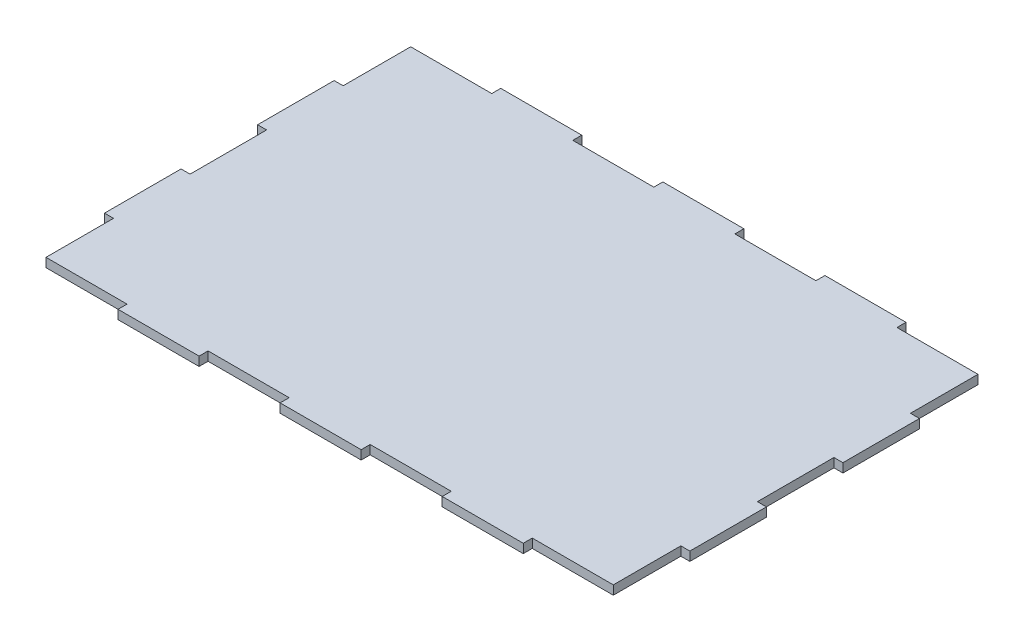
SolidWorks part; units mm, degrees
material "A-Glass Fiber"
ref_plane "Front Plane" through (0, 0, 0) normal (0, 0, 1) x (1, 0, 0)
ref_plane "Top Plane" through (0, 0, 0) normal (0, 1, 0) x (1, 0, 0)
ref_plane "Right Plane" through (0, 0, 0) normal (1, 0, 0) x (0, 0, -1)
sketch "Sketch1" plane through (0, 0, 0) normal (0, 1, 0) x (1, 0, 0)
  line L4 (45.72, 215.9) -> (-45.72, 215.9)
  line L5 (-45.72, 215.9) -> (-45.72, 205.74)
  line L6 (-45.72, 205.74) -> (45.72, 205.74)
  line L7 (45.72, 205.74) -> (45.72, 215.9)
  line L8 (228.6, 215.9) -> (137.16, 215.9)
  line L9 (137.16, 215.9) -> (137.16, 205.74)
  line L10 (137.16, 205.74) -> (228.6, 205.74)
  line L11 (228.6, 205.74) -> (228.6, 215.9)
  line L12 (330.2, 43.18) -> (330.2, 129.54)
  line L13 (330.2, 129.54) -> (320.04, 129.54)
  line L15 (320.04, 43.18) -> (330.2, 43.18)
  line L16 (330.2, -129.54) -> (330.2, -43.18)
  line L17 (330.2, -43.18) -> (320.04, -43.18)
  line L18 (320.04, -43.18) -> (320.04, -129.54)
  line L19 (320.04, -129.54) -> (330.2, -129.54)
  line L20 (228.6, -205.74) -> (137.16, -205.74)
  line L21 (137.16, -205.74) -> (137.16, -215.9)
  line L22 (137.16, -215.9) -> (228.6, -215.9)
  line L23 (228.6, -215.9) -> (228.6, -205.74)
  line L24 (45.72, -205.74) -> (-45.72, -205.74)
  line L25 (-45.72, -205.74) -> (-45.72, -215.9)
  line L26 (-45.72, -215.9) -> (45.72, -215.9)
  line L27 (45.72, -215.9) -> (45.72, -205.74)
  line L28 (-137.16, -205.74) -> (-228.6, -205.74)
  line L29 (-228.6, -205.74) -> (-228.6, -215.9)
  line L30 (-228.6, -215.9) -> (-137.16, -215.9)
  line L31 (-137.16, -215.9) -> (-137.16, -205.74)
  line L32 (-137.16, 215.9) -> (-228.6, 215.9)
  line L33 (-228.6, 215.9) -> (-228.6, 205.74)
  line L34 (-228.6, 205.74) -> (-137.16, 205.74)
  line L35 (-137.16, 205.74) -> (-137.16, 215.9)
  line L36 (-320.04, -129.54) -> (-320.04, -43.18)
  line L37 (-320.04, -43.18) -> (-330.2, -43.18)
  line L38 (-330.2, -43.18) -> (-330.2, -129.54)
  line L39 (-330.2, -129.54) -> (-320.04, -129.54)
  line L40 (-320.04, 43.18) -> (-320.04, 129.54)
  line L41 (-320.04, 129.54) -> (-330.2, 129.54)
  line L42 (-330.2, 129.54) -> (-330.2, 43.18)
  line L43 (-330.2, 43.18) -> (-320.04, 43.18)
  line L45 (-320.04, -205.74) -> (-330.2, -205.74)
  line L46 (228.6, -205.74) -> (320.04, -205.74)
  line L47 (320.04, 205.74) -> (330.2, 205.74)
  line L49 (330.2, 215.9) -> (330.2, -215.9)
  line L50 (330.2, -215.9) -> (-330.2, -215.9)
  line L51 (-330.2, 215.9) -> (-330.2, -215.9)
  line L52 (45.72, 215.9) -> (-45.72, 215.9)
  line L53 (-45.72, 215.9) -> (-45.72, 205.74)
  line L54 (-45.72, 205.74) -> (45.72, 205.74)
  line L55 (45.72, 205.74) -> (45.72, 215.9)
  line L56 (228.6, 215.9) -> (137.16, 215.9)
  line L57 (137.16, 215.9) -> (137.16, 205.74)
  line L58 (137.16, 205.74) -> (228.6, 205.74)
  line L59 (228.6, 205.74) -> (228.6, 215.9)
  line L60 (330.2, 43.18) -> (330.2, 129.54)
  line L61 (330.2, 129.54) -> (320.04, 129.54)
  line L62 (320.04, 129.54) -> (320.04, 43.18)
  line L63 (320.04, 43.18) -> (330.2, 43.18)
  line L64 (330.2, -129.54) -> (330.2, -43.18)
  line L65 (330.2, -43.18) -> (320.04, -43.18)
  line L66 (320.04, -43.18) -> (320.04, -129.54)
  line L67 (320.04, -129.54) -> (330.2, -129.54)
  line L68 (228.6, -205.74) -> (137.16, -205.74)
  line L69 (137.16, -205.74) -> (137.16, -215.9)
  line L70 (137.16, -215.9) -> (228.6, -215.9)
  line L71 (228.6, -215.9) -> (228.6, -205.74)
  line L72 (45.72, -205.74) -> (-45.72, -205.74)
  line L73 (-45.72, -205.74) -> (-45.72, -215.9)
  line L74 (-45.72, -215.9) -> (45.72, -215.9)
  line L75 (45.72, -215.9) -> (45.72, -205.74)
  line L76 (-137.16, -205.74) -> (-228.6, -205.74)
  line L77 (-228.6, -205.74) -> (-228.6, -215.9)
  line L78 (-228.6, -215.9) -> (-137.16, -215.9)
  line L79 (-137.16, -215.9) -> (-137.16, -205.74)
  line L80 (-137.16, 215.9) -> (-228.6, 215.9)
  line L81 (-228.6, 215.9) -> (-228.6, 205.74)
  line L82 (-228.6, 205.74) -> (-137.16, 205.74)
  line L83 (-137.16, 205.74) -> (-137.16, 215.9)
  line L84 (-320.04, -129.54) -> (-320.04, -43.18)
  line L85 (-320.04, -43.18) -> (-330.2, -43.18)
  line L86 (-330.2, -43.18) -> (-330.2, -129.54)
  line L87 (-330.2, -129.54) -> (-320.04, -129.54)
  line L88 (-320.04, 43.18) -> (-320.04, 129.54)
  line L89 (-320.04, 129.54) -> (-330.2, 129.54)
  line L90 (-330.2, 129.54) -> (-330.2, 43.18)
  line L91 (-330.2, 43.18) -> (-320.04, 43.18)
  line L92 (228.6, -205.74) -> (228.6, -215.9)
  line L93 (-320.04, -205.74) -> (-320.04, -129.54)
  line L94 (45.72, 215.9) -> (137.16, 215.9)
  line L95 (320.04, 205.74) -> (320.04, 129.54)
  line L97 (-228.6, 205.74) -> (-228.6, 215.9)
  line L99 (-330.2, 205.74) -> (-330.2, 215.9)
  line L100 (-137.16, 215.9) -> (-45.72, 215.9)
  line L101 (-137.16, 215.9) -> (-137.16, 205.74)
  line L102 (-137.16, 205.74) -> (-45.72, 205.74)
  line L103 (-45.72, 215.9) -> (-45.72, 205.74)
  line L104 (45.72, 215.9) -> (45.72, 205.74)
  line L105 (45.72, 205.74) -> (137.16, 205.74)
  line L106 (137.16, 215.9) -> (137.16, 205.74)
  line L107 (228.6, 215.9) -> (320.04, 215.9)
  line L108 (228.6, 215.9) -> (228.6, 205.74)
  line L109 (228.6, 205.74) -> (320.04, 205.74)
  line L110 (320.04, 215.9) -> (320.04, 205.74)
  line L111 (320.04, 215.9) -> (330.2, 215.9)
  line L112 (320.04, 215.9) -> (320.04, 205.74)
  line L113 (320.04, 205.74) -> (330.2, 205.74)
  line L114 (330.2, 215.9) -> (330.2, 205.74)
  line L115 (320.04, 129.54) -> (330.2, 129.54)
  line L116 (330.2, 205.74) -> (330.2, 129.54)
  line L117 (320.04, 43.18) -> (330.2, 43.18)
  line L118 (320.04, 43.18) -> (320.04, -43.18)
  line L119 (320.04, -43.18) -> (330.2, -43.18)
  line L120 (330.2, 43.18) -> (330.2, -43.18)
  line L121 (320.04, -129.54) -> (330.2, -129.54)
  line L122 (320.04, -129.54) -> (320.04, -205.74)
  line L123 (320.04, -205.74) -> (330.2, -205.74)
  line L124 (330.2, -129.54) -> (330.2, -205.74)
  line L125 (228.6, -215.9) -> (320.04, -215.9)
  line L126 (320.04, -205.74) -> (320.04, -215.9)
  line L127 (137.16, -205.74) -> (45.72, -205.74)
  line L128 (137.16, -205.74) -> (137.16, -215.9)
  line L129 (137.16, -215.9) -> (45.72, -215.9)
  line L130 (45.72, -205.74) -> (45.72, -215.9)
  line L131 (-45.72, -215.9) -> (-137.16, -215.9)
  line L132 (-45.72, -215.9) -> (-45.72, -205.74)
  line L133 (-45.72, -205.74) -> (-137.16, -205.74)
  line L134 (-137.16, -215.9) -> (-137.16, -205.74)
  line L135 (-228.6, -215.9) -> (-320.04, -215.9)
  line L136 (-228.6, -215.9) -> (-228.6, -205.74)
  line L137 (-228.6, -205.74) -> (-320.04, -205.74)
  line L138 (-320.04, -215.9) -> (-320.04, -205.74)
  line L139 (-320.04, -205.74) -> (-330.2, -205.74)
  line L140 (-320.04, -205.74) -> (-320.04, -215.9)
  line L141 (-320.04, -215.9) -> (-330.2, -215.9)
  line L142 (-330.2, -205.74) -> (-330.2, -215.9)
  line L143 (-320.04, -129.54) -> (-330.2, -129.54)
  line L144 (-330.2, -205.74) -> (-330.2, -129.54)
  line L145 (-330.2, -43.18) -> (-320.04, -43.18)
  line L146 (-330.2, -43.18) -> (-330.2, 43.18)
  line L147 (-330.2, 43.18) -> (-320.04, 43.18)
  line L148 (-320.04, -43.18) -> (-320.04, 43.18)
  line L149 (-320.04, 129.54) -> (-330.2, 129.54)
  line L150 (-320.04, 129.54) -> (-320.04, 205.74)
  line L151 (-320.04, 205.74) -> (-330.2, 205.74)
  line L152 (-330.2, 129.54) -> (-330.2, 205.74)
  line L153 (-330.2, 205.74) -> (-320.04, 205.74)
  line L154 (-330.2, 205.74) -> (-330.2, 215.9)
  line L155 (-330.2, 215.9) -> (-320.04, 215.9)
  line L156 (-320.04, 205.74) -> (-320.04, 215.9)
  line L157 (-228.6, 205.74) -> (-320.04, 205.74)
  line L158 (-228.6, 205.74) -> (-228.6, 215.9)
  line L159 (-228.6, 215.9) -> (-320.04, 215.9)
  line L160 (-320.04, 205.74) -> (-320.04, 215.9)
  dimension "D1" = 660.4
  dimension "D2" = 431.8
  dimension "D3" = 10.16
  dimension "D4" = 10.16
  dimension "D5" = 10.16
  dimension "D6" = 10.16
extrude "Boss-Extrude1" add sketch "Sketch1" along normal blind 10.16 contours L34 L157 L150 L40 L148 L36 L93 L137 L28 L133 L24 L127 L20 L46 L122 L18 L118 L62 L95 L109 L10 L105 L6 L102 | L42 L43 L40 L41 | L38 L39 L36 L37 | L30 L31 L28 L29 | L26 L27 L24 L25 | L22 L23 L20 L21 | L18 L19 L16 L17 | L13 L62 L15 L12 | L34 L35 L32 L33 | L6 L7 L4 L5 | L10 L11 L8 L9
